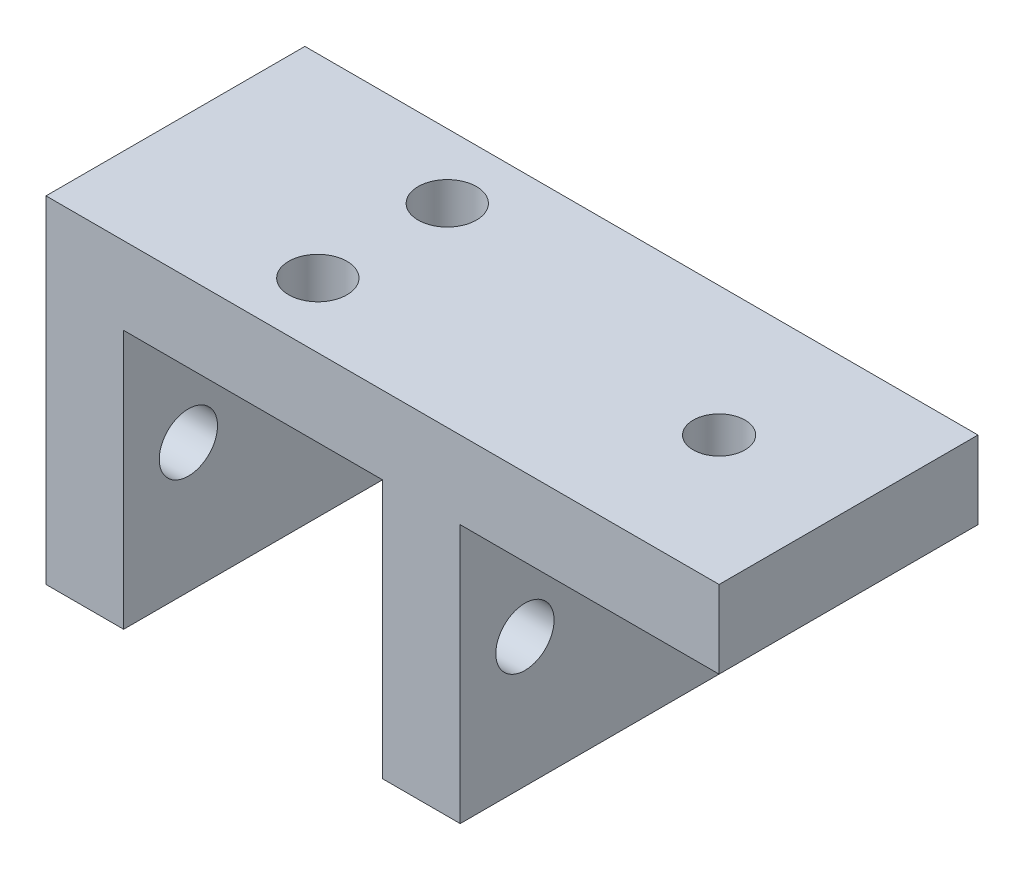
SolidWorks part; units mm, degrees
ref_plane "Front Plane" through (0, 0, 0) normal (0, 0, 1) x (1, 0, 0)
ref_plane "Top Plane" through (0, 0, 0) normal (0, 1, 0) x (1, 0, 0)
ref_plane "Right Plane" through (0, 0, 0) normal (1, 0, 0) x (0, 0, -1)
sketch "Sketch7" plane through (0, 0, 0) normal (0, 0, 1) x (1, 0, 0)
  line L0 (-52, -26) -> (-52, 0)
  line L2 (-20, -6) -> (-20, -26)
  line L3 (-20, -26) -> (-26, -26)
  line L4 (-26, -26) -> (-26, -6)
  line L5 (-26, -6) -> (-46, -6)
  line L6 (-46, -6) -> (-46, -26)
  line L7 (-46, -26) -> (-52, -26)
  line L8 (-20, -6) -> (0, -6)
  line L9 (0, -6) -> (0, 0)
  line L10 (-52, 0) -> (0, 0)
  dimension "D1" = 20
  dimension "D2" = 6
  dimension "D3" = 6
  dimension "D4" = 20
  dimension "D5" = 6
  dimension "D6" = 20
extrude "Boss-Extrude3" add sketch "Sketch7" along normal blind 20
sketch "Sketch9" plane through (-46, 0, 0) normal (1, 0, 0) x (0, 0, -1)
  line L0 (-15, -16) -> (-20, -16) construction
  line L1 (-20, -26) -> (-20, -6) construction
  line L2 (-10, -6) -> (-10, -26) construction
  line L3 (-20, -6) -> (0, -6) construction
  line L4 (-20, -26) -> (0, -26) construction
  line L5 (-15, -16) -> (-10, -16) construction
  circle A0 centre (-15, -16) radius 2.25
  circle A1 centre (-5, -16) radius 2.25
  dimension "D1" = 4.5
extrude "Cut-Extrude1" cut sketch "Sketch9" against normal through all both and the other way through all
sketch "Sketch10" plane through (0, -6, 0) normal (0, -1, 0) x (1, 0, 0)
  line L0 (-46, 10) -> (-26, 10) construction
  line L1 (-46, 20) -> (-46, 0) construction
  line L2 (-26, 20) -> (-26, 0) construction
  line L3 (-36, 10) -> (-36, 5) construction
  line L4 (-36, 5) -> (-36, 0) construction
  line L5 (-46, 0) -> (-26, 0) construction
  circle A0 centre (-36, 5) radius 2.25
  circle A1 centre (-36, 15) radius 2.25
  dimension "D1" = 4.5
extrude "Cut-Extrude2" cut sketch "Sketch10" against normal through all both
sketch "Sketch11" plane through (0, -6, 0) normal (0, -1, 0) x (1, 0, 0)
  line L0 (-20, 20) -> (0, 0) construction
  circle A0 centre (-10, 10) radius 2
  dimension "D1" = 4
extrude "Cut-Extrude3" cut sketch "Sketch11" against normal through all both
